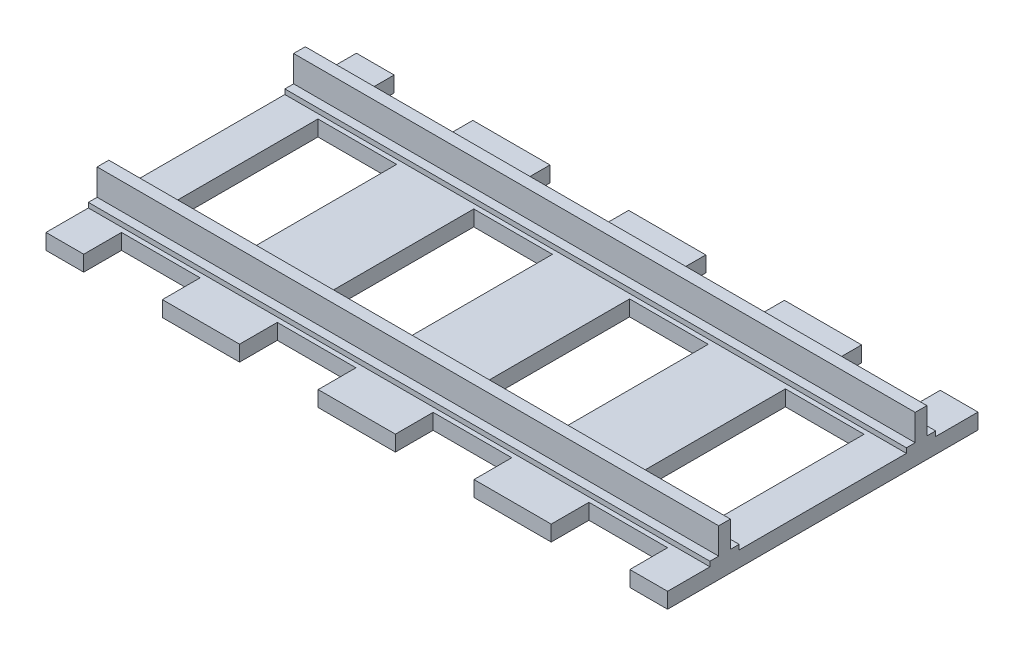
SolidWorks part; units mm, degrees
ref_plane "Front Plane" through (0, 0, 0) normal (0, 0, 1) x (1, 0, 0)
ref_plane "Top Plane" through (0, 0, 0) normal (0, 1, 0) x (1, 0, 0)
ref_plane "Right Plane" through (0, 0, 0) normal (1, 0, 0) x (0, 0, -1)
sketch "Sketch1" plane through (0, 0, 0) normal (0, 1, 0) x (1, 0, 0)
  line L0 (24.075, -31.875) -> (24.075, 31.875)
  line L1 (-63.825, 31.875) -> (63.825, 31.875)
  line L2 (-63.825, 31.875) -> (-63.825, -31.875)
  line L3 (-63.825, -31.875) -> (63.825, -31.875)
  line L4 (63.825, 31.875) -> (63.825, -31.875)
  line L5 (-63.825, 31.875) -> (63.825, -31.875) construction
  line L6 (-63.825, -31.875) -> (63.825, 31.875) construction
  line L7 (-7.925, -31.875) -> (7.925, -31.875)
  line L8 (-7.925, -31.875) -> (-7.925, 31.875)
  line L9 (-7.925, 31.875) -> (7.925, 31.875)
  line L10 (7.925, -31.875) -> (7.925, 31.875)
  line L11 (-7.925, -31.875) -> (7.925, 31.875) construction
  line L12 (-7.925, 31.875) -> (7.925, -31.875) construction
  line L13 (39.925, -31.875) -> (39.925, 31.875)
  line L14 (56.075, -31.875) -> (56.075, 31.875)
  line L15 (71.925, -31.875) -> (71.925, 31.875)
  line L16 (0, 31.875) -> (0, -31.875) construction
  line L17 (-56.075, -31.875) -> (-56.075, 31.875)
  line L18 (-39.925, -31.875) -> (-39.925, 31.875)
  line L19 (-24.075, -31.875) -> (-24.075, 31.875)
  line L20 (-63.825, 0) -> (63.825, 0) construction
  line L21 (-63.825, 24.125) -> (63.825, 24.125)
  line L22 (-63.825, 24.125) -> (-63.825, 16.225)
  line L23 (-63.825, 16.225) -> (63.825, 16.225)
  line L24 (63.825, 24.125) -> (63.825, 16.225)
  line L25 (-63.825, 24.125) -> (63.825, 16.225) construction
  line L26 (-63.825, 16.225) -> (63.825, 24.125) construction
  line L27 (-63.825, -24.125) -> (63.825, -24.125)
  line L28 (-63.825, -16.225) -> (63.825, -16.225)
  point P0 (0, 0)
  point P6 (0, 0)
  point P27 (0, 20.175)
  dimension "D1" = 63.75
  dimension "D2" = 127.65
  dimension "D3" = 15.85
  dimension "D5" = 32
  dimension "D6" = 7.9
  dimension "D7" = 48.25
  dimension "D4" = 3
extrude "Boss-Extrude1" add sketch "Sketch1" along normal blind 3.2 contours L2 L28 L17 L23 | L2 L23 L17 L21 | L2 L21 L17 L1 | L28 L2 L27 L17 | L27 L2 L3 L17 | L17 L23 L18 L21 | L28 L17 L27 L18 | L27 L18 L3 L19 | L28 L18 L27 L19 | L18 L28 L19 L23 | L18 L23 L19 L21 | L18 L21 L19 L1 | L19 L23 L8 L21 | L28 L19 L27 L8 | L28 L8 L27 L10 | L27 L8 L3 L10 | L8 L23 L10 L21 | L8 L28 L10 L23 | L8 L21 L10 L1 | L0 L21 L13 L1 | L0 L23 L13 L21 | L0 L28 L13 L23 | L28 L0 L27 L13 | L27 L0 L3 L13 | L10 L23 L0 L21 | L28 L10 L27 L0 | L28 L13 L27 L14 | L13 L23 L14 L21 | L14 L21 L4 L1 | L14 L23 L4 L21 | L14 L28 L4 L23 | L28 L14 L27 L4 | L27 L14 L3 L4
sketch "Sketch2" plane through (0, 3.2, 0) normal (0, 1, 0) x (1, 0, 0)
  line L0 (0, 31.875) -> (0, -31.875) construction
  line L1 (-7.925, 31.875) -> (7.925, 31.875) construction
  line L2 (-7.925, -31.875) -> (7.925, -31.875) construction
  line L3 (-63.825, 0) -> (63.825, 0) construction
  line L4 (-63.825, 31.875) -> (-63.825, -31.875) construction
  line L5 (63.825, 31.875) -> (63.825, -31.875) construction
  line L6 (-7.925, 24.125) -> (-7.925, 16.225) construction
  line L7 (-63.825, 20.175) -> (63.825, 20.175) construction
  line L8 (-63.825, -23.175) -> (63.825, -23.175)
  line L9 (-63.825, 23.175) -> (63.825, 23.175)
  line L10 (-63.825, 23.175) -> (-63.825, 17.175)
  line L11 (-63.825, 17.175) -> (63.825, 17.175)
  line L12 (63.825, 23.175) -> (63.825, 17.175)
  line L13 (-63.825, 23.175) -> (63.825, 17.175) construction
  line L14 (-63.825, 17.175) -> (63.825, 23.175) construction
  line L15 (63.825, -23.175) -> (63.825, -17.175)
  line L16 (-63.825, -17.175) -> (63.825, -17.175)
  line L17 (-63.825, -23.175) -> (-63.825, -17.175)
  point P18 (-7.925, 20.175)
  point P19 (0, 20.175)
  dimension "D1" = 6
extrude "Boss-Extrude2" add sketch "Sketch2" along normal blind 1
sketch "Sketch3" plane through (0, 4.2, 0) normal (0, 1, 0) x (1, 0, 0)
  line L0 (0, 31.875) -> (0, -31.875) construction
  line L1 (-7.925, 31.875) -> (7.925, 31.875) construction
  line L2 (-7.925, -31.875) -> (7.925, -31.875) construction
  line L3 (-63.825, 20.175) -> (63.825, 20.175) construction
  line L4 (-63.825, 23.175) -> (-63.825, 17.175) construction
  line L5 (63.825, 17.175) -> (63.825, 23.175) construction
  line L6 (-63.825, 0) -> (63.825, 0) construction
  line L7 (-63.825, 21.375) -> (63.825, 21.375)
  line L8 (-63.825, 21.375) -> (-63.825, 18.975)
  line L9 (-63.825, 18.975) -> (63.825, 18.975)
  line L10 (63.825, 21.375) -> (63.825, 18.975)
  line L11 (-63.825, 21.375) -> (63.825, 18.975) construction
  line L12 (-63.825, 18.975) -> (63.825, 21.375) construction
  line L13 (-63.825, 17.175) -> (-63.825, -17.175) construction
  line L14 (63.825, 17.175) -> (63.825, -17.175) construction
  line L15 (63.825, -21.375) -> (63.825, -18.975)
  line L16 (-63.825, -21.375) -> (63.825, -21.375)
  line L17 (-63.825, -18.975) -> (63.825, -18.975)
  line L18 (-63.825, -21.375) -> (-63.825, -18.975)
  point P12 (0, 20.175)
  dimension "D1" = 2.4
extrude "Boss-Extrude3" add sketch "Sketch3" along normal offset from surface (5.4 mm away) 9.6 up to face at (0, 0, 0)
